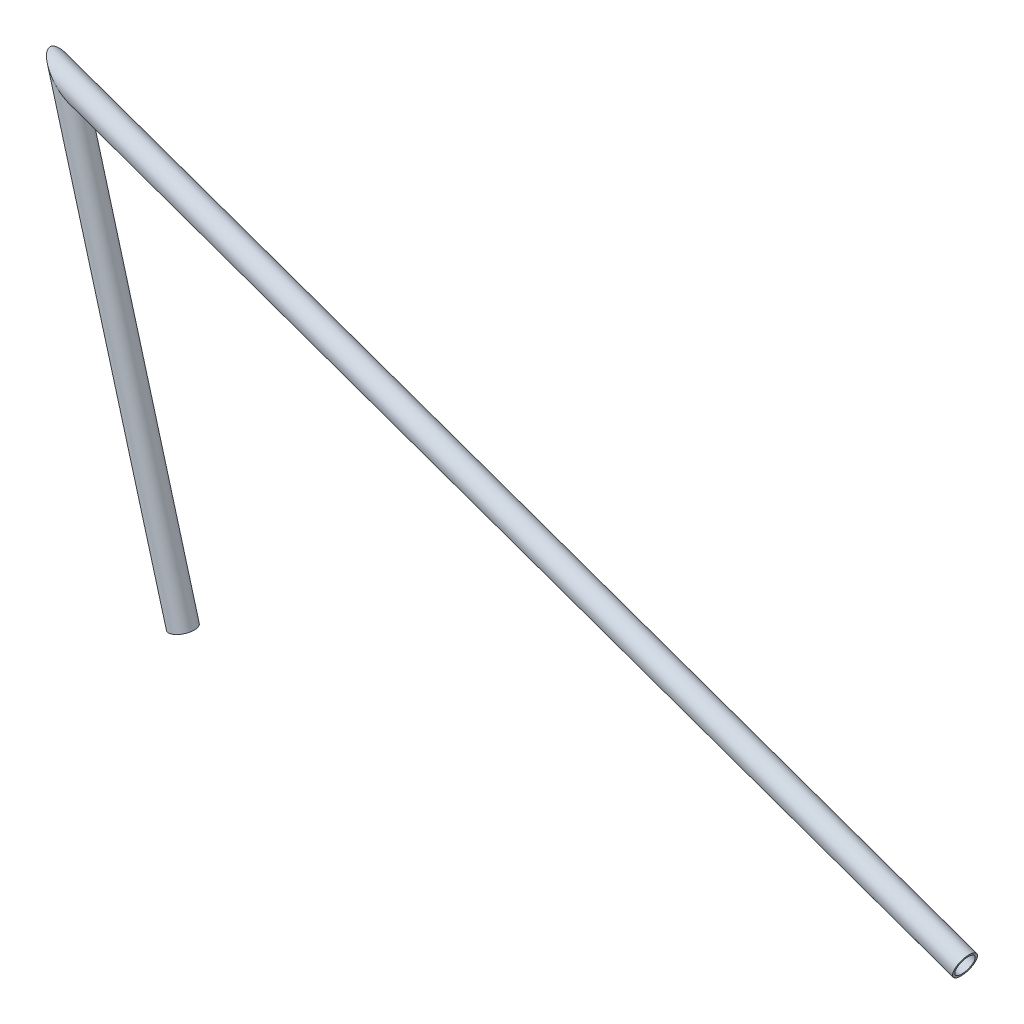
SolidWorks part; units mm, degrees
ref_plane "Front" through (0, 0, 0) normal (0, 0, 1) x (1, 0, 0)
ref_plane "Top" through (0, 0, 0) normal (0, 1, 0) x (1, 0, 0)
ref_plane "Right" through (0, 0, 0) normal (1, 0, 0) x (0, 0, -1)
sketch "Sketch1" plane through (0, 0, 0) normal (0, 0, 1) x (1, 0, 0)
  line L0 (0, 0) -> (599.4988, -213.2972)
  line L1 (0, 0) -> (77, -278.8495)
  line L3 (0, 0) -> (685.4798, -243.8886) construction
  line L4 (0, 0) -> (599.4988, -213.2972) construction
  line L5 (599.4988, -213.2972) -> (0, -288.5099) construction
  line L6 (0, 0) -> (0, -288.5099) construction
  line L8 (-263.7506, -288.5099) -> (839.6254, -288.5099) construction
  circle A0 centre (77, -278.8495) radius 14.6812 construction
  circle A1 centre (599.4988, -213.2972) radius 14.6812 construction
  dimension "D3" = 636.3132
  dimension "D4" = 29.3624
  dimension "D1" = 9.6604
  dimension "D2" = 288.5099
  dimension "D5" = 289.2854
other "Structural Member1"
ref_plane "Plane1" through (0, 0, 0) normal (0.2662, -0.9639, 0) x (0.9639, 0.2662, 0)
sketch "Sketch11" plane through (0, 0, 0) normal (0.2662, -0.9639, 0) x (0.9639, 0.2662, 0)
  circle A0 centre (0, 0) radius 6.4643
  circle A1 centre (0, 0) radius 7.9375
  point P5 (0, 0)
  dimension "Out_dia" = 15.875
  dimension "D1" = 1.4732
